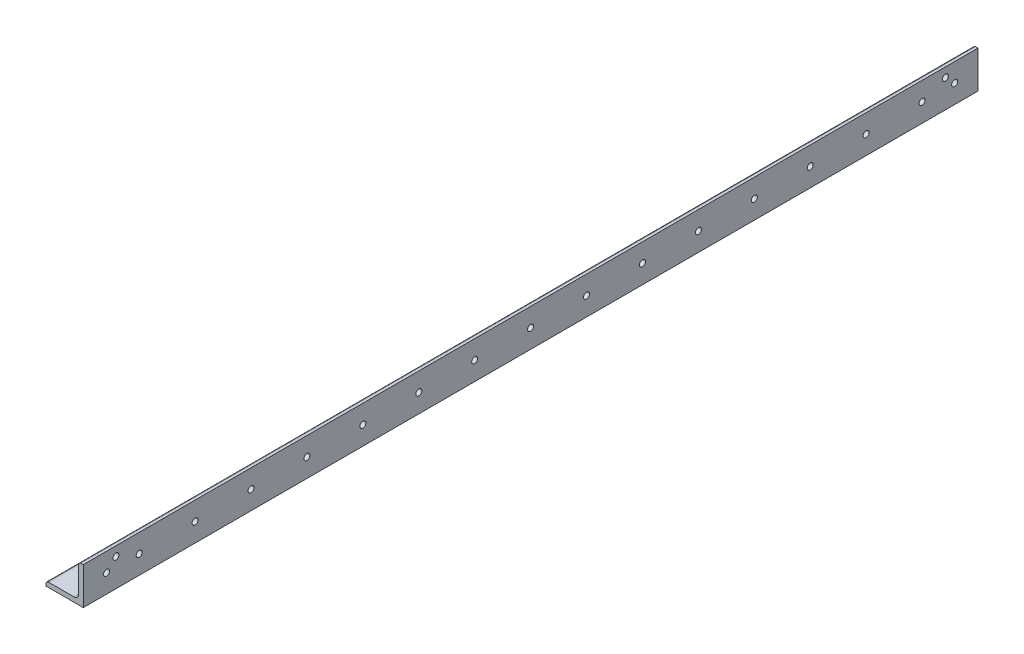
SolidWorks part; units mm, degrees
ref_plane "Front Plane" through (0, 0, 0) normal (0, 0, 1) x (1, 0, 0)
ref_plane "Top Plane" through (0, 0, 0) normal (0, 1, 0) x (1, 0, 0)
ref_plane "Right Plane" through (0, 0, 0) normal (1, 0, 0) x (0, 0, -1)
sketch "Sketch0" plane through (0, 0, 0) normal (0, 0, 1) x (1, 0, 0)
  line L0 (-12.7, -12.7) -> (12.7, -12.7)
  line L1 (12.7, -12.7) -> (12.7, 12.7)
  line L2 (12.7, 0) -> (0, 0) construction
  line L3 (0, 0) -> (0, -12.7) construction
  line L4 (9.525, -6.35) -> (9.525, 12.7) construction
  line L5 (6.35, -9.525) -> (-12.7, -9.525) construction
  arc A0 (9.525, -6.35) -> (6.35, -9.525) centre (6.35, -6.35) cw
  point P3 (8.5951, -8.5951)
  dimension "Inside Corner Radius" = 3.175
  dimension "Outside Height" = 25.4
  dimension "Inside Height" = 22.225
  dimension "Inside Width" = 22.225
  dimension "Wall Thickness" = 3.175
  dimension "D1" = 3.175
  dimension "Outside Width" = 25.4
sketch "Sketch1" plane through (0, 0, 0) normal (1, 0, 0) x (0, 0, -1)
  line L0 (304.8, 0) -> (-304.8, 0)
  point P4 (0, 0)
  dimension "Length" = 609.6
sketch "Sketch2" plane through (0, 0, 0) normal (0, 0, 1) x (1, 0, 0)
  line L0 (-12.7, -12.7) -> (12.7, -12.7)
  line L1 (12.7, -12.7) -> (12.7, 12.7)
  line L2 (12.7, 12.7) -> (9.525, 12.7) construction
  line L3 (9.525, 11.1125) -> (9.525, -6.35)
  line L4 (6.35, -9.525) -> (-11.1125, -9.525)
  line L5 (-12.7, -12.7) -> (-12.7, -9.525) construction
  line L6 (11.1125, 12.7) -> (12.7, 12.7)
  line L7 (-12.7, -11.1125) -> (-12.7, -12.7)
  line L8 (12.7, 0) -> (0, 0) construction
  line L9 (0, 0) -> (0, -12.7) construction
  arc A0 (9.525, 11.1125) -> (11.1125, 12.7) centre (11.1125, 11.1125) cw
  arc A1 (-12.7, -11.1125) -> (-11.1125, -9.525) centre (-11.1125, -11.1125) cw
  arc A2 (9.525, -6.35) -> (6.35, -9.525) centre (6.35, -6.35) cw
  dimension "Inside Radius" = 3.175
  dimension "Height" = 25.4
  dimension "Width" = 25.4
  dimension "Thickness" = 3.175
extrude "Boss-Extrude1" add sketch "Sketch2" along normal mid plane 609.6
sketch "Break Locations" plane through (0, 0, 0) normal (1, 0, 0) x (0, 0, -1)
  line L0 (-278.892, 0) -> (278.892, 0)
  line L1 (-304.8, -12.7) -> (-304.8, 12.7) construction
  line L2 (304.8, -12.7) -> (304.8, 12.7) construction
  point P0 (-283.21, 0)
  point P1 (283.21, 0)
  point P10 (0, 0)
  point P11 (278.892, 0)
  point P13 (-278.892, 0)
  dimension "D1" = 21.59
  dimension "D2" = 21.59
  dimension "D3" = 25.908
sketch "Sketch11" plane through (12.7, 0, 0) normal (1, 0, 0) x (0, 0, -1)
  line L0 (304.8, -12.7) -> (304.8, 12.7) construction
  line L1 (0, 0) -> (0, 12.7) construction
  circle A0 centre (288.925, 0) radius 2.05
  circle A1 centre (282.575, 6.35) radius 2.05
  circle A2 centre (266.7, 0) radius 2.05
  circle A3 centre (228.6, 0) radius 2.05
  circle A4 centre (190.5, 0) radius 2.05
  circle A5 centre (152.4, 0) radius 2.05
  circle A6 centre (114.3, 0) radius 2.05
  circle A7 centre (76.2, 0) radius 2.05
  circle A8 centre (38.1, 0) radius 2.05
  circle A9 centre (0, 0) radius 2.05
  circle A10 centre (-38.1, 0) radius 2.05
  circle A11 centre (-76.2, 0) radius 2.05
  circle A12 centre (-114.3, 0) radius 2.05
  circle A13 centre (-152.4, 0) radius 2.05
  circle A14 centre (-190.5, 0) radius 2.05
  circle A15 centre (-228.6, 0) radius 2.05
  circle A16 centre (-266.7, 0) radius 2.05
  circle A17 centre (-282.575, 6.35) radius 2.05
  circle A18 centre (-288.925, 0) radius 2.05
  point P2 (0, 0)
  point P39 (0, -12.7)
  point P40 (0, 12.7)
  dimension "D1" = 4.1
  dimension "D2" = 15.875
  dimension "D3" = 6.35
  dimension "D4" = 6.35
  dimension "D5" = 38.1
  dimension "D7" = 38.1
  dimension "D6" = 15
extrude "Cut-Extrude1" cut sketch "Sketch11" against normal blind 50.8
equation "\"D1@Break Locations\" = .85 * \"Height@Sketch2\""
equation "\"D2@Break Locations\"=\"D1@Break Locations\""
equation "\"Thickness@Sketch2\" = \"Wall Thickness@Sketch0\""
equation "\"Height@Sketch2\" = \"Outside Height@Sketch0\""
equation "\"Width@Sketch2\" = \"Outside Width@Sketch0\""
equation "\"Inside Radius@Sketch2\" = \"Inside Corner Radius@Sketch0\""
equation "\"Length@Boss-Extrude1\" = \"Length@Sketch1\""
equation "\"D3@Break Locations\"=\"D2@Break Locations\"*1.2"
equation "\"D1@Sketch0\"=\"Wall Thickness@Sketch0\""
